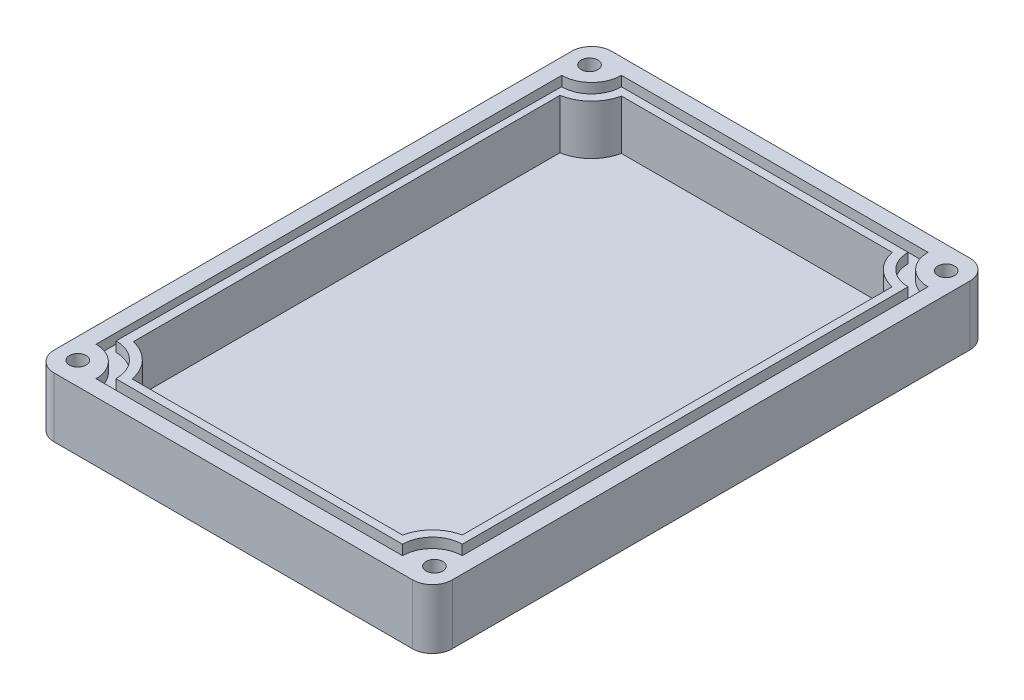
SolidWorks part; units mm, degrees
ref_plane "Front Plane" through (0, 0, 0) normal (0, 0, 1) x (1, 0, 0)
ref_plane "Top Plane" through (0, 0, 0) normal (0, 1, 0) x (1, 0, 0)
ref_plane "Right Plane" through (0, 0, 0) normal (1, 0, 0) x (0, 0, -1)
sketch "Wall" plane through (0, 0, 0) normal (0, 1, 0) x (1, 0, 0)
  line L0 (0, -70) -> (0, 70) construction
  line L1 (-50, 0) -> (50, 0) construction
  line L2 (-50, -70) -> (-50, 70)
  line L3 (-50, 70) -> (50, 70)
  line L4 (50, 70) -> (50, -70)
  line L5 (50, -70) -> (-50, -70)
  line L6 (0, 70) -> (0, 66) construction
  line L7 (-50, 0) -> (-46, 0) construction
  line L8 (-46, -66) -> (-46, 66)
  line L9 (46, 66) -> (-46, 66)
  line L10 (46, 66) -> (46, -66)
  line L11 (-46, -66) -> (46, -66)
  arc A0 (-38.5, 66) -> (-46, 58.5) centre (-46, 66) cw
  arc A1 (38.5, 66) -> (46, 58.5) centre (46, 66) ccw
  arc A2 (-46, -58.5) -> (-38.5, -66) centre (-46, -66) cw
  arc A3 (38.5, -66) -> (46, -58.5) centre (46, -66) cw
  point P4 (0, 0)
  point P8 (0, 0)
  point P10 (-50, 0)
  point P17 (-46, 0)
  point P20 (0, 66)
  dimension "D5" = 7.5
  dimension "D1" = 140
  dimension "D2" = 100
  dimension "D3" = 4
  dimension "D4" = 4
sketch "Base" plane through (0, 0, 0) normal (0, 1, 0) x (1, 0, 0)
  line L0 (-50, -70) -> (-50, 70)
  line L1 (50, -70) -> (50, 70)
  line L3 (-50, -70) -> (50, -70)
  line L9 (-50, 70) -> (50, 70)
  point P4 (-50, 0)
  point P10 (50, 0)
extrude "Bottom" add sketch "Base" against normal blind 2.5
extrude "Walls" add sketch "Wall" along normal blind 12.5 contours L5 L4 L3 L2 L11 L8 L9 L10 | A2 L8 L11 | A3 L11 L10 | A0 L9 L8 | L9 A1 L10
ref_plane "Drill" through (0, 12.5, 0) normal (0, -1, 0) x (-1, 0, 0)
fillet "MainFillet" radius 5 4 edges at (-50, 5, -70) (50, 5, -70) (-50, 5, 70) (50, 5, 70)
sketch "DrillHoles" plane through (0, 12.5, 0) normal (0, -1, 0) x (-1, 0, 0)
  line L0 (0, -66) -> (0, 66) construction
  line L1 (-38.5, 66) -> (38.5, 66) construction
  line L2 (-46, -66) -> (46, 66) construction
  line L3 (46, -66) -> (-46, 66) construction
  line L4 (46, 66) -> (44.7992, 64.2772) construction
  line L5 (-46, 66) -> (-44.7992, 64.2772) construction
  line L6 (-46, -66) -> (-44.7992, -64.2772) construction
  line L7 (46, -66) -> (44.7992, -64.2772) construction
  circle A0 centre (44.7992, 64.2772) radius 2.1
  circle A1 centre (44.7992, -64.2772) radius 2.1
  circle A2 centre (-44.7992, -64.2772) radius 2.1
  circle A3 centre (-44.7992, 64.2772) radius 2.1
  point P6 (0, 0)
  point P10 (0, 0)
  point P14 (0, 0)
  dimension "D1" = 2.1
  dimension "D2" = 2.1
  dimension "D3" = 2.1
  dimension "D4" = 2.1
extrude "Drilling" cut sketch "DrillHoles" along normal blind 45
sketch "Gasket" plane through (0, 0, 0) normal (0, 1, 0) x (1, 0, 0)
  line L0 (46, 66) -> (-46, -66) construction
  line L1 (46, -66) -> (-46, 66) construction
  line L2 (-46, 66) -> (46, 66) construction
  line L3 (46, 66) -> (46, -66) construction
  line L4 (46, -66) -> (-46, -66) construction
  line L5 (-46, -66) -> (-46, 66) construction
  line L6 (-38.5, 66) -> (38.5, 66)
  line L7 (46, 58.5) -> (46, -58.5)
  line L8 (38.5, -66) -> (-38.5, -66)
  line L9 (-46, -58.5) -> (-46, 58.5)
  line L10 (-46, 0) -> (-43.5, 0) construction
  line L11 (46, 0) -> (43.5, 0) construction
  line L12 (0, -66) -> (0, -63.5) construction
  line L13 (0, 66) -> (0, 63.5) construction
  line L14 (44.3594, 63.5) -> (-43.5, 63.5) construction
  line L15 (-43.5, 63.5) -> (-44.2576, -63.5) construction
  line L16 (-44.2576, -63.5) -> (43.5, -63.5) construction
  line L17 (43.5, -63.5) -> (43.5, 63.5) construction
  line L18 (-36, -63.5) -> (36, -63.5)
  line L19 (43.5, -56) -> (43.5, 56)
  line L20 (36, 63.5) -> (-36, 63.5)
  line L21 (-43.5447, 56.0001) -> (-44.2083, -55.2426)
  circle A0 centre (-44.7992, -64.2772) radius 2.1 construction
  circle A1 centre (-44.7992, 64.2772) radius 2.1 construction
  arc A2 (-46, 58.5) -> (-38.5, 66) centre (-46, 66) ccw
  arc A3 (38.5, 66) -> (46, 58.5) centre (46, 66) ccw
  arc A4 (46, -58.5) -> (38.5, -66) centre (46, -66) ccw
  arc A5 (-38.5, -66) -> (-46, -58.5) centre (-46, -66) ccw
  arc A6 (-36, 63.5) -> (-43.5447, 56.0001) centre (-43.5, 63.5) cw
  arc A7 (36, 63.5) -> (43.5, 56) centre (43.5, 63.5) ccw
  arc A8 (36, -63.5) -> (43.5, -56) centre (43.5, -63.5) cw
  arc A9 (-36, -63.5) -> (-44.2083, -55.2426) centre (-44.2576, -63.5) ccw
  point P43 (0.4297, 63.5)
  dimension "D6" = 2.5
  dimension "D7" = 2.5
  dimension "D8" = 2.5
  dimension "D9" = 2.5
  dimension "D1" = 2.5
  dimension "D2" = 2.5
  dimension "D3" = 2.5
  dimension "D4" = 2.5
  dimension "D5" = 0.4297
ref_plane "Plane1" through (0, -2.5, 0) normal (0, 1, 0) x (1, 0, 0)
sketch "Sketch8" plane through (0, -2.5, 0) normal (0, 1, 0) x (1, 0, 0)
  circle A0 centre (-44.7992, 64.2772) radius 3
  circle A1 centre (44.7992, 64.2772) radius 3
  circle A2 centre (-44.7992, -64.2772) radius 3
  circle A4 centre (44.7992, -64.2772) radius 3
  dimension "D1" = 6
  dimension "D2" = 6
  dimension "D3" = 6
  dimension "D4" = 6
extrude "Cut-Extrude2" cut sketch "Sketch8" along normal blind 2.5
sketch "Extrusion" plane through (0, 12.5, 0) normal (0, -1, 0) x (-1, 0, 0)
  line L0 (43.5447, 56.0001) -> (44.2083, -55.2426)
  line L1 (36, -63.5) -> (-36, -63.5)
  line L2 (-43.5, -56) -> (-43.5, 56)
  line L3 (-36, 63.5) -> (36, 63.5)
  line L4 (0, 63.5) -> (0, 61.5) construction
  line L5 (-43.5, 0) -> (-41.5, 0) construction
  line L6 (0, -63.5) -> (0, -61.5) construction
  line L7 (43.8765, 0.3788) -> (41.8765, 0.3788) construction
  line L8 (41.8765, -53.2426) -> (41.8765, 54.0001)
  line L9 (-41.5, -54) -> (-41.5, 54)
  line L10 (34, 61.5) -> (-34, 61.5)
  line L11 (34, -61.5) -> (-34, -61.5)
  arc A0 (44.2083, -55.2426) -> (36, -63.5) centre (44.2576, -63.5) ccw
  arc A1 (-36, -63.5) -> (-43.5, -56) centre (-43.5, -63.5) ccw
  arc A2 (-43.5, 56) -> (-36, 63.5) centre (-43.5, 63.5) ccw
  arc A3 (43.5447, 56.0001) -> (36, 63.5) centre (43.5, 63.5) cw
  arc A4 (34, 61.5) -> (41.8765, 53.9285) centre (43.5, 63.5) ccw
  arc A5 (41.8765, -53.2426) -> (33.9191, -61.5) centre (44.2576, -63.5) ccw
  arc A6 (-41.5, -54) -> (-34, -61.5) centre (-43.5, -63.5) cw
  arc A7 (-34, 61.5) -> (-41.5, 54) centre (-43.5, 63.5) cw
  point P35 (41.8765, 0.3788)
  point P38 (-41.5, 0)
  point P44 (0, -61.5)
  point P45 (0, 61.5)
  dimension "D1" = 2
  dimension "D2" = 2
  dimension "D3" = 2
  dimension "D4" = 2
  dimension "D5" = 2
  dimension "D6" = 2
  dimension "D7" = 2
  dimension "D8" = 2
extrude "Boss-Extrude1" add sketch "Extrusion" along normal blind 12.5
extrude "Boss-Extrude2" add sketch "Gasket" along normal blind 10
